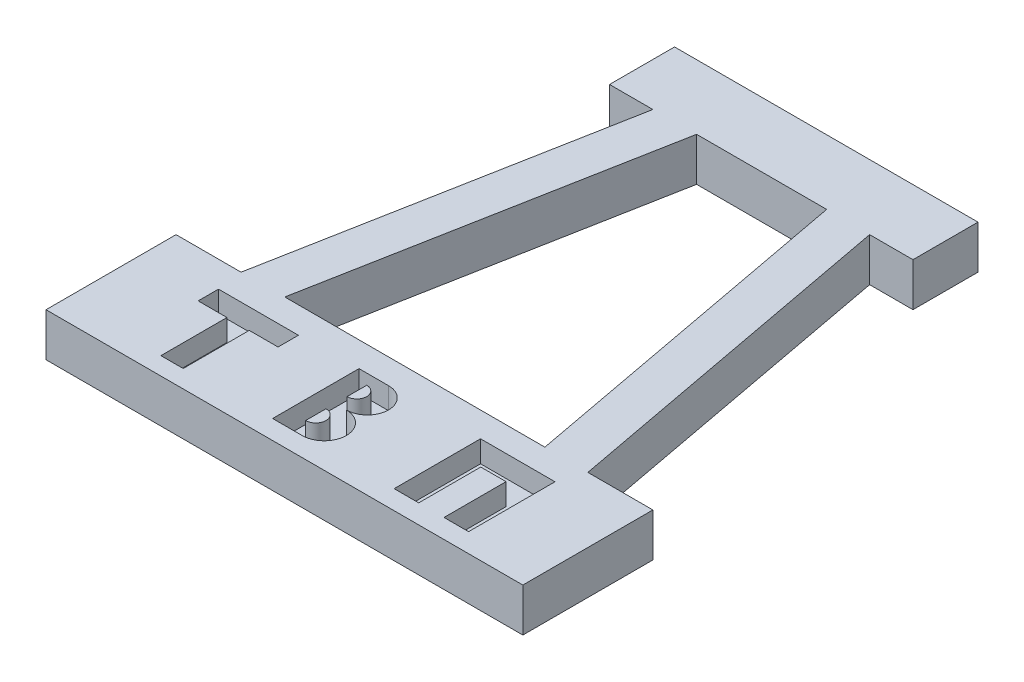
SolidWorks part; units mm, degrees
ref_plane "Front Plane" through (0, 0, 0) normal (0, 0, 1) x (1, 0, 0)
ref_plane "Top Plane" through (0, 0, 0) normal (0, 1, 0) x (1, 0, 0)
ref_plane "Right Plane" through (0, 0, 0) normal (1, 0, 0) x (0, 0, -1)
sketch "Sketch1" plane through (0, 0, 0) normal (0, 1, 0) x (1, 0, 0)
  line L0 (0, 0) -> (0, 242.6905) construction
  line L1 (-69.85, 0) -> (0, 0)
  line L2 (69.85, 0) -> (69.85, 38.1)
  line L3 (-44.45, 158.75) -> (-44.45, 139.7)
  line L4 (44.45, 158.75) -> (44.45, 139.7)
  line L5 (-69.85, 0) -> (-69.85, 38.1)
  line L6 (-69.85, 38.1) -> (-50.8, 38.1)
  line L7 (-44.45, 158.75) -> (0, 158.75)
  line L8 (69.85, 38.1) -> (50.8, 38.1)
  line L9 (-50.8, 38.1) -> (-31.75, 139.7)
  line L10 (-31.75, 139.7) -> (-44.45, 139.7)
  line L11 (50.8, 38.1) -> (31.75, 139.7)
  line L12 (31.75, 139.7) -> (44.45, 139.7)
  line L13 (0, 158.75) -> (44.45, 158.75)
  line L14 (0, 0) -> (69.85, 0)
  dimension "D1" = 44.45
  dimension "D2" = 44.45
  dimension "D3" = 69.85
  dimension "D4" = 69.85
  dimension "D5" = 19.05
  dimension "D6" = 19.05
  dimension "D7" = 38.1
  dimension "D8" = 38.1
  dimension "D9" = 101.6
  dimension "D10" = 19.05
  dimension "D11" = 19.05
  dimension "D12" = 12.7
  dimension "D13" = 12.7
sketch "Sketch3" plane through (0, 0, 0) normal (0, 1, 0) x (1, 0, 0)
  line L1 (0, 0) -> (0, 242.6905) construction
  line L2 (0, 38.2099) -> (-38.1, 38.2099)
  line L3 (-38.1, 38.2099) -> (-19.05, 139.8099)
  line L4 (0, 38.2099) -> (38.1, 38.2099)
  line L5 (38.1, 38.2099) -> (19.05, 139.8099)
  line L6 (19.05, 139.8099) -> (0, 139.8099)
  line L7 (0, 139.8099) -> (-19.05, 139.8099)
  line L8 (-50.8, 38.1) -> (-31.75, 139.7) construction
  dimension "D1" = 38.1
  dimension "D2" = 38.1
  dimension "D3" = 19.05
  dimension "D4" = 19.05
extrude "Boss-Extrude1" add sketch "Sketch1" along normal blind 12.7
extrude "Cut-Extrude2" cut sketch "Sketch3" against normal blind 25.4 and the other way blind 33.274
sketch "Sketch4" plane through (0, 12.7, 0) normal (0, 1, 0) x (1, 0, 0)
  line L0 (-69.85, 19.05) -> (69.85, 19.05) construction
  line L1 (-69.85, 38.1) -> (-69.85, 0) construction
  line L2 (69.85, 0) -> (69.85, 38.1) construction
  line L3 (-38.1, 38.2099) -> (-38.1, 0) construction
  line L4 (-69.85, 0) -> (69.85, 0) construction
  line L5 (38.1, 38.2099) -> (38.1, 0) construction
  line L6 (-38.1, 30.4972) -> (-26.3961, 30.4972)
  line L7 (-26.3961, 30.4972) -> (-26.3961, 24.5289)
  line L8 (-26.3961, 24.5289) -> (-34.8339, 24.5289)
  line L9 (-34.8339, 24.5289) -> (-34.8339, 5.1836)
  line L10 (-34.8339, 5.1836) -> (-38.1, 5.1836)
  line L11 (-38.1, 5.1836) -> (-41.3661, 5.1836)
  line L12 (-41.3661, 5.1836) -> (-41.3661, 24.5289)
  line L13 (-41.3661, 24.5289) -> (-49.8039, 24.5289)
  line L14 (-49.8039, 24.5289) -> (-49.8039, 30.4972)
  line L15 (-49.8039, 30.4972) -> (-38.1, 30.4972)
  point P20 (0, 0)
extrude "Cut-Extrude3" cut sketch "Sketch4" against normal blind 6.35
sketch "Sketch5" plane through (0, 12.7, 0) normal (0, 1, 0) x (1, 0, 0)
  line L0 (-9.0553, 5.5952) -> (-9.0553, 30.9088)
  line L1 (-9.0553, 30.9088) -> (-0.4116, 30.9088)
  line L2 (-9.0553, 5.5952) -> (-0.4116, 5.5952)
  line L3 (-3.7044, 9.9171) -> (-3.7044, 15.8853)
  line L4 (-3.7044, 22.0593) -> (-3.7044, 27.8218)
  arc A0 (-0.4116, 30.9088) -> (-0.4116, 18.5607) centre (-0.4116, 24.7347) cw
  arc A1 (-0.4116, 18.5607) -> (-0.4116, 5.5952) centre (-0.4116, 12.078) cw
  arc A2 (-3.7044, 27.8218) -> (-3.7044, 22.0593) centre (-3.7044, 24.9405) cw
  arc A3 (-3.7044, 15.8853) -> (-3.7044, 9.9171) centre (-3.7044, 12.9012) cw
extrude "Cut-Extrude4" cut sketch "Sketch5" against normal blind 6.35
sketch "Sketch6" plane through (0, 12.7, 0) normal (0, 1, 0) x (1, 0, 0)
  line L0 (26.5484, 5.5952) -> (33.7514, 5.5952)
  line L1 (33.7514, 5.5952) -> (33.7514, 23.7696)
  line L2 (33.7514, 23.7696) -> (41.1603, 23.7696)
  line L3 (41.1603, 23.7696) -> (41.1603, 5.5952)
  line L4 (41.1603, 5.5952) -> (48.3633, 5.5952)
  line L5 (48.3633, 5.5952) -> (48.3633, 30.9088)
  line L6 (48.3633, 30.9088) -> (26.5484, 30.9088)
  line L7 (26.5484, 30.9088) -> (26.5484, 5.5952)
extrude "Cut-Extrude5" cut sketch "Sketch6" against normal blind 6.35
